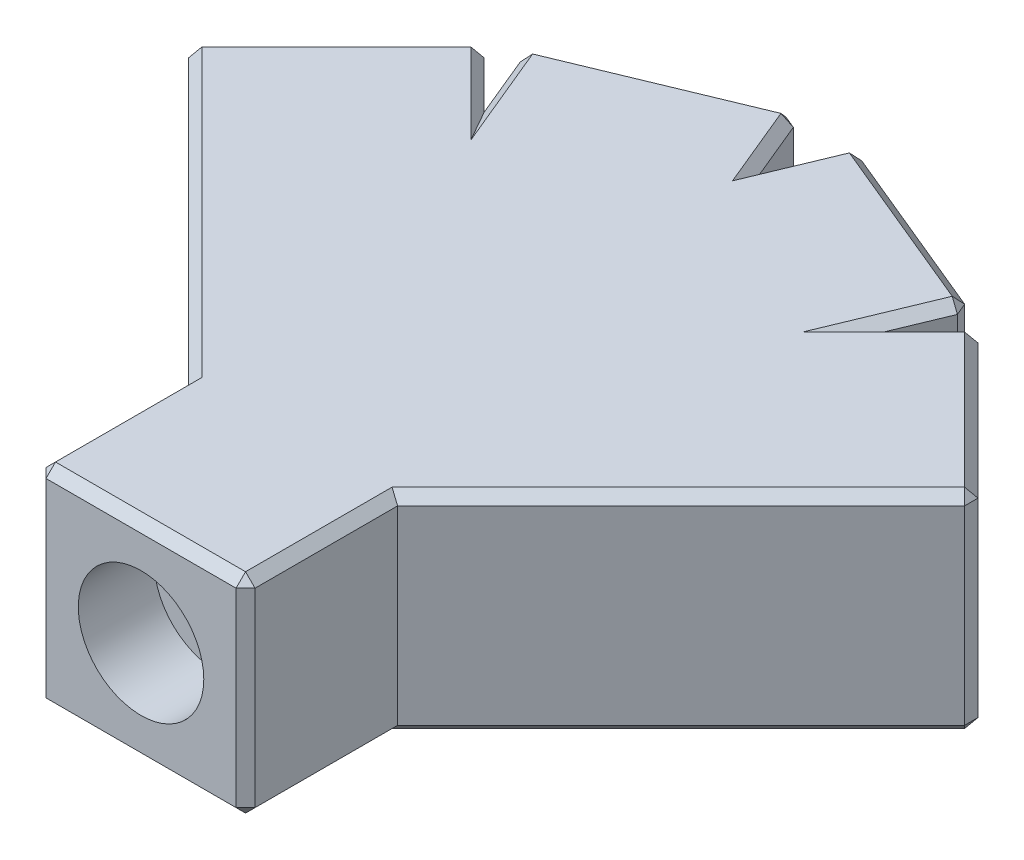
SolidWorks part; units mm, degrees
ref_plane "Front Plane" through (0, 0, 0) normal (0, 0, 1) x (1, 0, 0)
ref_plane "Top Plane" through (0, 0, 0) normal (0, 1, 0) x (1, 0, 0)
ref_plane "Right Plane" through (0, 0, 0) normal (1, 0, 0) x (0, 0, -1)
sketch "Sketch2" plane through (0, 0, 0) normal (0, 1, 0) x (1, 0, 0)
  line L0 (0, 24.4285) -> (-10.1627, 20.219)
  line L1 (-10.1627, 20.219) -> (-17.9408, 12.4408)
  line L2 (-17.9408, 12.4408) -> (-5.5, 0)
  line L3 (-5.5, 0) -> (5.5, 0)
  line L4 (0, 0) -> (0, 24.4285) construction
  line L5 (17.9408, 12.4408) -> (5.5, 0)
  line L6 (10.1627, 20.219) -> (17.9408, 12.4408)
  line L7 (0, 24.4285) -> (10.1627, 20.219)
  line L8 (0, 24.4285) -> (51.7778, 24.4285) construction
  point P9 (0, 0)
  dimension "D1" = 22.5
  dimension "D2" = 45
  dimension "D3" = 11
extrude "Boss-Extrude1" add sketch "Sketch2" along normal blind 11
sketch "Sketch5" plane through (15.1908, 0, -15.1908) normal (0.7071, 0, -0.7071) x (-0.7071, 0, -0.7071)
  line L0 (-3.8891, 0) -> (7.1109, 11) construction
  circle A0 centre (1.6109, 5.5) radius 1.25
  dimension "D1" = 2.5
extrude "Cut-Extrude3" cut sketch "Sketch5" against normal blind 21
sketch "Sketch6" plane through (8.6368, 0, -20.8511) normal (0.3827, 0, -0.9239) x (-0.9239, 0, -0.3827)
  line L0 (-1.6516, 0) -> (9.3484, 11) construction
  circle A0 centre (3.8484, 5.5) radius 1.25
  dimension "D1" = 2.5
extrude "Cut-Extrude4" cut sketch "Sketch6" against normal blind 14
sketch "Sketch7" plane through (-8.6368, 0, -20.8511) normal (-0.3827, 0, -0.9239) x (-0.9239, 0, 0.3827)
  line L0 (-9.3484, 0) -> (1.6516, 11) construction
  circle A0 centre (-3.8484, 5.5) radius 1.25
  dimension "D1" = 2.5
extrude "Cut-Extrude5" cut sketch "Sketch7" against normal blind 14
sketch "Sketch8" plane through (-15.1908, 0, -15.1908) normal (-0.7071, 0, -0.7071) x (-0.7071, 0, 0.7071)
  line L0 (-7.1109, 0) -> (3.8891, 11) construction
  circle A0 centre (-1.6109, 5.5) radius 1.25
  dimension "D1" = 2.5
extrude "Cut-Extrude6" cut sketch "Sketch8" against normal blind 21
sketch "Sketch9" plane through (0, 0, 0) normal (0, 0, 1) x (1, 0, 0)
  line L1 (-5.5, 11) -> (5.5, 11)
  line L2 (-5.5, 11) -> (-5.5, 0)
  line L3 (-5.5, 0) -> (5.5, 0)
  line L4 (5.5, 11) -> (5.5, 0)
extrude "Boss-Extrude2" add sketch "Sketch9" along normal blind 8
sketch "Sketch10" plane through (0, 0, 8) normal (0, 0, 1) x (1, 0, 0)
  line L0 (-5.5, 0) -> (5.5, 11) construction
  circle A0 centre (0, 5.5) radius 1.25
  dimension "D1" = 2.5
extrude "Cut-Extrude7" cut sketch "Sketch10" against normal blind 18
sketch "Sketch12" plane through (0, 0, 8) normal (0, 0, 1) x (1, 0, 0)
  circle A0 centre (0, 5.5) radius 3.302
  dimension "D1" = 6.604
extrude "Cut-Extrude9" cut sketch "Sketch12" against normal blind 4
sketch "Sketch18" plane through (15.1908, 0, -15.1908) normal (0.7071, 0, -0.7071) x (-0.7071, 0, -0.7071)
  line L1 (-3.8891, 11) -> (7.1109, 11)
  line L2 (-3.8891, 11) -> (-3.8891, 0)
  line L3 (-3.8891, 0) -> (7.1109, 0)
  line L4 (7.1109, 11) -> (7.1109, 0)
  circle A0 centre (1.6109, 5.5) radius 3.302
  dimension "D1" = 6.604
extrude "Boss-Extrude3" add sketch "Sketch18" along normal blind 4 contours L2 L1 L4 L3 | A0
sketch "Sketch19" plane through (8.6368, 0, -20.8511) normal (0.3827, 0, -0.9239) x (-0.9239, 0, -0.3827)
  line L1 (-1.6516, 11) -> (9.3484, 11)
  line L2 (-1.6516, 11) -> (-1.6516, 0)
  line L3 (-1.6516, 0) -> (9.3484, 0)
  line L4 (9.3484, 11) -> (9.3484, 0)
  circle A0 centre (3.8484, 5.5) radius 3.302
  dimension "D1" = 6.604
extrude "Boss-Extrude4" add sketch "Sketch19" along normal blind 4
sketch "Sketch20" plane through (-8.6368, 0, -20.8511) normal (-0.3827, 0, -0.9239) x (-0.9239, 0, 0.3827)
  line L2 (-9.3484, 11) -> (1.6516, 11)
  line L3 (-9.3484, 11) -> (-9.3484, 0)
  line L4 (-9.3484, 0) -> (1.6516, 0)
  line L5 (1.6516, 11) -> (1.6516, 0)
  circle A0 centre (-3.8484, 5.5) radius 3.302
  circle A1 centre (-3.8484, 5.5) radius 1.25 construction
  dimension "D1" = 6.604
extrude "Boss-Extrude5" add sketch "Sketch20" along normal blind 4
sketch "Sketch22" plane through (-15.1908, 0, -15.1908) normal (-0.7071, 0, -0.7071) x (-0.7071, 0, 0.7071)
  line L1 (-7.1109, 11) -> (3.8891, 11)
  line L2 (-7.1109, 11) -> (-7.1109, 0)
  line L3 (-7.1109, 0) -> (3.8891, 0)
  line L4 (3.8891, 11) -> (3.8891, 0)
  circle A0 centre (-1.6109, 5.5) radius 3.302
  dimension "D1" = 6.604
extrude "Boss-Extrude7" add sketch "Sketch22" along normal blind 4
chamfer "Chamfer1" distance 0.5 angle 45 40 edges at (16.8802, 11, -19.1584) (5.5, 11, 4) (0, 11, 8) (-5.5, 11, 4) (-16.8802, 11, -19.1584) (-11.5769, 11, -21.6332) (-10.928, 11, -22.0668) (-6.6121, 11, -26.0193) (-0.7654, 11, -26.2763) (0.7654, 11, -26.2763) (6.6121, 11, -26.0193) (10.928, 11, -22.0668) (11.5769, 11, -21.6332) (-5.5, 0, 4) (-5.5, 5.5, 8) (0, 0, 8) (5.5, 5.5, 8) (5.5, 0, 4) (-20.7693, 5.5, -15.2693) (-16.8802, 0, -19.1584) (-12.9911, 5.5, -23.0475) (-11.5769, 0, -21.6332) (-10.928, 0, -22.0668) (-11.6934, 5.5, -23.9145) (-6.6121, 0, -26.0193) (-1.5307, 5.5, -28.1241) (-0.7654, 0, -26.2763) (0.7654, 0, -26.2763) (1.5307, 5.5, -28.1241) (6.6121, 0, -26.0193) (11.6934, 5.5, -23.9145) (10.928, 0, -22.0668) (11.5769, 0, -21.6332) (12.9911, 5.5, -23.0475) (16.8802, 0, -19.1584) (20.7693, 5.5, -15.2693) (13.1346, 11, -7.6346) (-13.1346, 11, -7.6346) (-13.1346, 0, -7.6346) (13.1346, 0, -7.6346)
